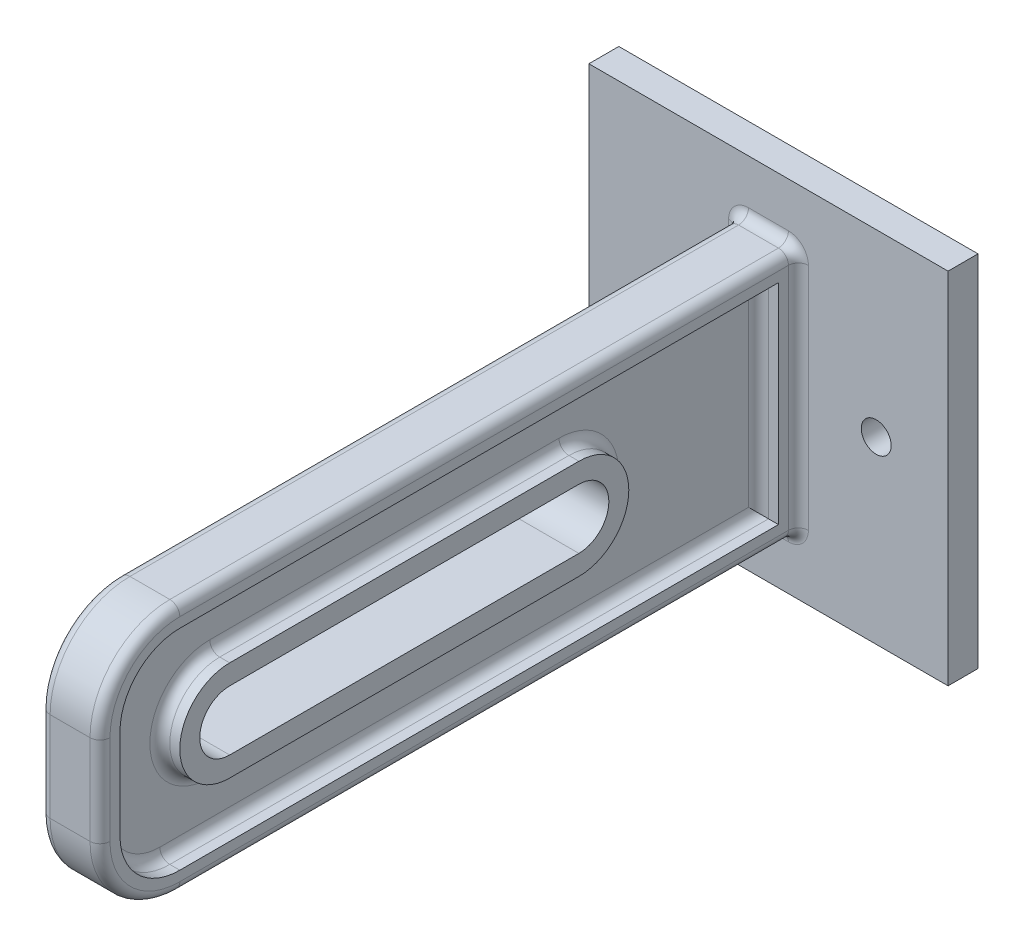
SolidWorks part; units mm, degrees
ref_plane "Front Plane" through (0, 0, 0) normal (0, 0, 1) x (1, 0, 0)
ref_plane "Top Plane" through (0, 0, 0) normal (0, 1, 0) x (1, 0, 0)
ref_plane "Right Plane" through (0, 0, 0) normal (1, 0, 0) x (0, 0, -1)
sketch "Sketch1" plane through (0, 0, 0) normal (0, 0, 1) x (1, 0, 0)
  line L1 (-18, -18) -> (18, -18)
  line L2 (-18, -18) -> (-18, 18)
  line L3 (-18, 18) -> (18, 18)
  line L4 (18, -18) -> (18, 18)
  line L5 (-18, -18) -> (18, 18) construction
  line L6 (-18, 18) -> (18, -18) construction
  point P0 (0, 0)
  dimension "D1" = 36
  dimension "D2" = 36
extrude "Boss-Extrude1" add sketch "Sketch1" along normal blind 3
sketch "Sketch2" plane through (0, 0, 3) normal (0, 0, 1) x (1, 0, 0)
  line L0 (0, 0) -> (23.1958, 0) construction
  circle A0 centre (10.7983, 0) radius 1.5
  circle A1 centre (-9.2017, 0) radius 1.5
  dimension "D1" = 3
  dimension "D2" = 20
extrude "Cut-Extrude1" cut sketch "Sketch2" against normal through all
sketch "Sketch3" plane through (0, 0, 3) normal (0, 0, 1) x (1, 0, 0)
  line L1 (3, -12.5) -> (-3, -12.5)
  line L2 (3, -12.5) -> (3, 12.5)
  line L3 (3, 12.5) -> (-3, 12.5)
  line L4 (-3, -12.5) -> (-3, 12.5)
  line L5 (3, -12.5) -> (-3, 12.5) construction
  line L6 (3, 12.5) -> (-3, -12.5) construction
  point P0 (0, 0)
  dimension "D1" = 6
  dimension "D2" = 25
extrude "Boss-Extrude2" add sketch "Sketch3" along normal blind 70
sketch "Sketch6" plane through (0, 0, 0) normal (1, 0, 0) x (0, 0, -1)
  line L0 (0, 0) -> (-85, 0) construction
  line L2 (-25, 3) -> (-60, 3)
  line L4 (-25, -3) -> (-60, -3)
  line L6 (-25, 3) -> (-60, -3) construction
  line L7 (-25, -3) -> (-60, 3) construction
  line L8 (-73, 12.5) -> (-73, -12.5) construction
  arc A0 (-60, 3) -> (-60, -3) centre (-60, 0) ccw
  arc A1 (-25, 3) -> (-25, -3) centre (-25, 0) cw
  point P3 (-42.5, 0)
  point P8 (-63, 0)
  dimension "D2" = 3
  dimension "D3" = 10
  dimension "D1" = 35
extrude "Cut-Extrude2" cut sketch "Sketch6" against normal through all and the other way blind 41
fillet "Fillet1" radius 8 2 edges at (0, -12.5, 73) (0, 12.5, 73)
sketch "Sketch7" plane through (-3, 0, 0) normal (-1, 0, 0) x (0, 0, 1)
  line L11 (60, 5) -> (25, 5)
  line L12 (25, -5) -> (60, -5)
  line L13 (60, 5) -> (25, 5)
  line L14 (25, -5) -> (60, -5)
  line L32 (65, 10.5) -> (5, 10.5)
  line L33 (5, 10.5) -> (5, -10.5)
  line L34 (5, -10.5) -> (65, -10.5)
  line L35 (71, -4.5) -> (71, 4.5)
  line L36 (65, 10.5) -> (5, 10.5)
  line L37 (5, 10.5) -> (5, -10.5)
  line L38 (5, -10.5) -> (65, -10.5)
  line L39 (71, -4.5) -> (71, 4.5)
  arc A12 (25, 5) -> (25, -5) centre (25, 0) ccw
  arc A13 (60, -5) -> (60, 5) centre (60, 0) ccw
  arc A14 (25, 5) -> (25, -5) centre (25, 0) ccw
  arc A15 (60, -5) -> (60, 5) centre (60, 0) ccw
  arc A22 (71, 4.5) -> (65, 10.5) centre (65, 4.5) ccw
  arc A23 (65, -10.5) -> (71, -4.5) centre (65, -4.5) ccw
  arc A24 (71, 4.5) -> (65, 10.5) centre (65, 4.5) ccw
  arc A25 (65, -10.5) -> (71, -4.5) centre (65, -4.5) ccw
  dimension "D1" = 2
  dimension "D2" = 2
extrude "Cut-Extrude3" cut sketch "Sketch7" against normal blind 2
mirror "Mirror1" about plane through (0, 0, 0) normal (1, 0, 0) of "Cut-Extrude3"
fillet "Fillet2" radius 1 34 edges at (3, 0, 3) (0, 12.5, 3) (0, -12.5, 3) (-1, -5, 42.5) (-1, 0, 20) (-1, 5, 42.5) (1, -5, 42.5) (1, 0, 20) (1, 5, 42.5) (1, 10.5, 35) (1, 8.7426, 69.2426) (1, 0, 71) (1, -8.7426, 69.2426) (-1, -10.5, 35) (-1, -8.7426, 69.2426) (-1, 0, 71) (-1, 8.7426, 69.2426) (-3, 12.5, 34) (-3, 10.1569, 70.6569) (-3, -12.5, 34) (-3, -10.1569, 70.6569) (3, -12.5, 34) (3, -10.1569, 70.6569) (3, 12.5, 34) (3, 10.1569, 70.6569) (-1, 0, 65) (1, 0, 65) (1, -10.5, 35) (1, 0, 5) (-1, 10.5, 35) (-3, 0, 3) (-1, 0, 5) (-3, 0, 73) (3, 0, 73)
